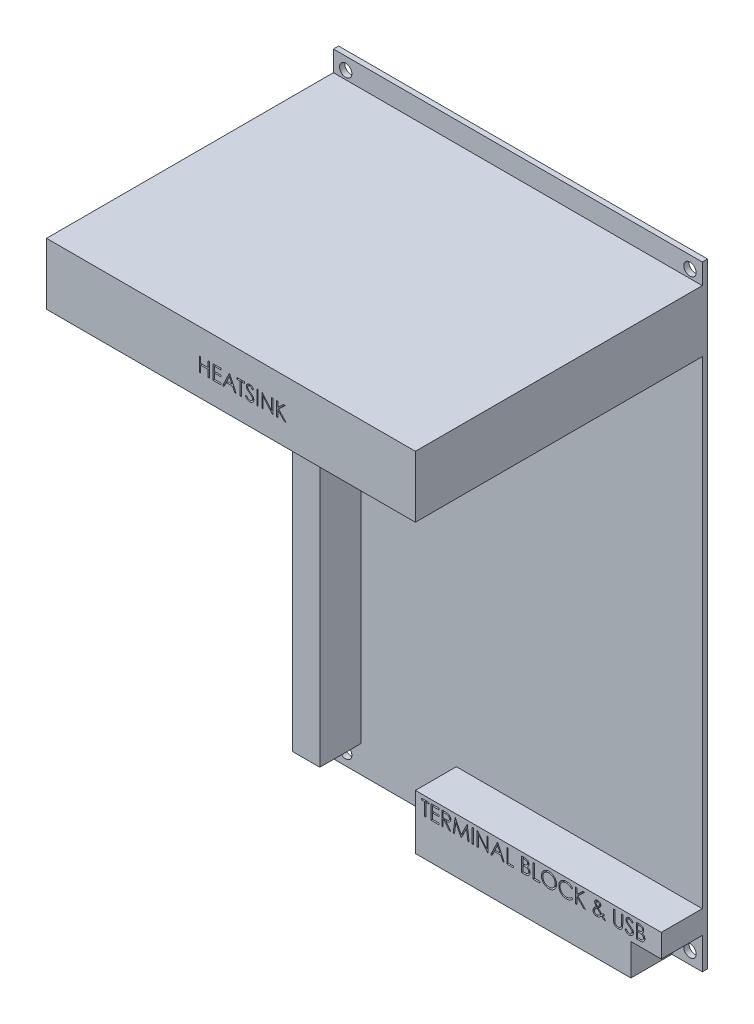
SolidWorks part; units mm, degrees
ref_plane "Front Plane" through (0, 0, 0) normal (0, 0, 1) x (1, 0, 0)
ref_plane "Top Plane" through (0, 0, 0) normal (0, 1, 0) x (1, 0, 0)
ref_plane "Right Plane" through (0, 0, 0) normal (1, 0, 0) x (0, 0, -1)
sketch "Sketch1" plane through (0, 0, 0) normal (0, 0, 1) x (1, 0, 0)
  line L1 (0, 0) -> (90, 0)
  line L2 (0, 0) -> (0, 150)
  line L3 (0, 150) -> (90, 150)
  line L4 (90, 0) -> (90, 150)
extrude "Boss-Extrude1" add sketch "Sketch1" along normal blind 1.27
sketch "Sketch2" plane through (0, 0, 1.27) normal (0, 0, 1) x (1, 0, 0)
  line L1 (0, 150) -> (0, 0) construction
  line L3 (90, 0) -> (90, 150) construction
  line L4 (0, 130) -> (90, 130)
  line L5 (0, 130) -> (0, 145)
  line L6 (0, 145) -> (90, 145)
  line L7 (90, 130) -> (90, 145)
extrude "Boss-Extrude2" add sketch "Sketch2" along normal blind 70
sketch "Sketch3" plane through (0, 0, 1.27) normal (0, 0, 1) x (1, 0, 0)
  circle A0 centre (3, 3) radius 1.5
  circle A1 centre (87, 3) radius 1.5
  circle A2 centre (3, 147) radius 1.5
  circle A3 centre (87, 147) radius 1.5
extrude "Cut-Extrude1" cut sketch "Sketch3" against normal blind 70
sketch "Sketch4" plane through (0, 0, 1.27) normal (0, 0, 1) x (1, 0, 0)
  line L0 (0, 6.5683) -> (6.6823, 6.5683)
  line L1 (0, 130) -> (0, 0) construction
  line L2 (6.6823, 6.5683) -> (6.6823, 71.5683)
  line L3 (6.6823, 71.5683) -> (0, 71.5683)
  line L4 (0, 71.5683) -> (0, 6.5683)
extrude "Boss-Extrude3" add sketch "Sketch4" along normal blind 10
sketch "Sketch5" plane through (0, 0, 1.27) normal (0, 0, 1) x (1, 0, 0)
  line L2 (30, 13.3479) -> (30, 0)
  line L3 (0, 0) -> (90, 0) construction
  line L4 (30, 0) -> (82.5945, 0)
  line L5 (82.5945, 0) -> (82.5945, 5.7915)
  line L6 (82.5945, 7.7106) -> (90, 7.7106)
  line L7 (90, 0) -> (90, 130) construction
  line L8 (90, 7.7106) -> (90, 13.3479)
  line L9 (90, 13.3479) -> (30, 13.3479)
  line L10 (82.5945, 5.7915) -> (82.5945, 7.7106)
extrude "Boss-Extrude4" add sketch "Sketch5" along normal blind 10
sketch "Sketch6" plane through (0, 0, 71.27) normal (0, 0, 1) x (1, 0, 0)
  text T0 "HEATSINK"
  text T1 "TERMINAL BLOCK & USB"
extrude "Cut-Extrude2" cut sketch "Sketch6" against normal blind 67
